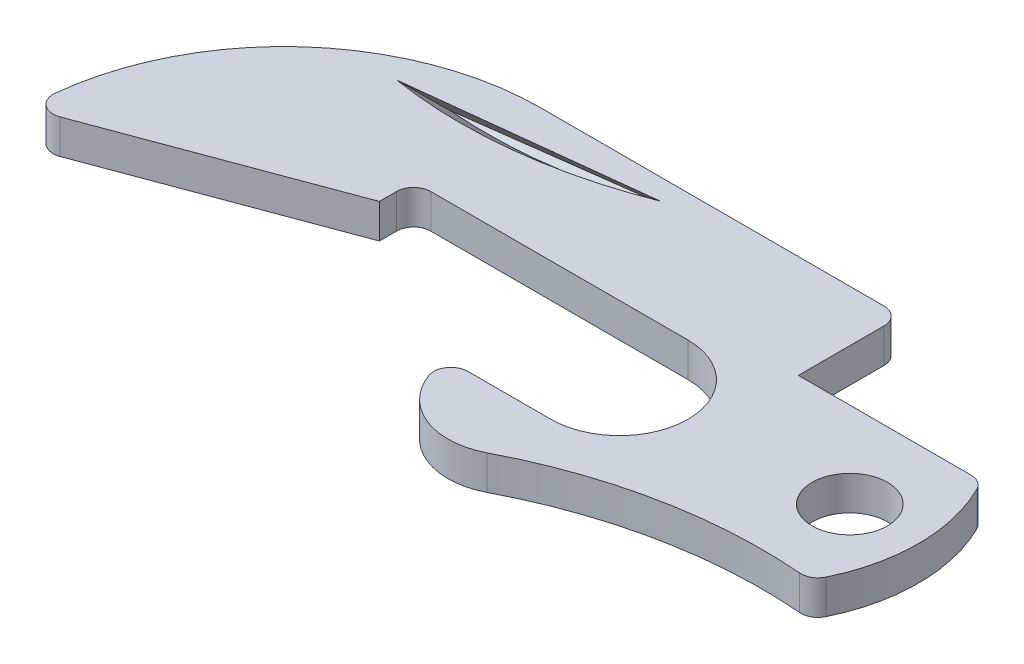
SolidWorks part; units mm, degrees
material "Stainless Steel (ferritic)"
ref_plane "Front Plane" through (0, 0, 0) normal (0, 0, 1) x (1, 0, 0)
ref_plane "Top Plane" through (0, 0, 0) normal (0, 1, 0) x (1, 0, 0)
ref_plane "Right Plane" through (0, 0, 0) normal (1, 0, 0) x (0, 0, -1)
sketch "Sketch1" plane through (0, 0, 0) normal (0, 1, 0) x (1, 0, 0)
  line L0 (0, 0) -> (-6.7693, 0)
  line L1 (-6.7693, 0) -> (-6.7693, 3.81)
  line L2 (-6.7693, 3.81) -> (-20.1043, 3.81)
  line L3 (-29.6293, -5.715) -> (-20.1043, -2.1795)
  line L4 (-20.1043, -2.1795) -> (-20.1043, -0.9095)
  line L5 (-20.1043, -0.9095) -> (-9.9443, -0.9095)
  line L6 (-9.9443, -5.9895) -> (-13.7543, -5.9895)
  line L7 (-29.6293, -5.715) -> (-29.6293, 7.3662) construction
  arc A0 (-20.1043, 3.81) -> (-29.6293, -5.715) centre (-20.1043, -5.715) ccw
  arc A1 (-9.9443, -0.9095) -> (-9.9443, -5.9895) centre (-9.9443, -3.4495) cw
  arc A4 (-10.0458, -8.2448) -> (0, -6.35) centre (-1.8666, -24.0317) cw
  arc A5 (0, -6.35) -> (0, 0) centre (-5.4993, -3.175) ccw
  arc A6 (-13.7543, -5.9895) -> (-10.0458, -8.2448) centre (-11.2143, -5.9895) ccw
  circle A7 centre (-1.6893, -3.175) radius 1.397
  point P19 (-7.4043, -3.4495)
  point P22 (0.8507, -3.175)
  dimension "D2" = 6.35
  dimension "D6" = 2.54
  dimension "D8" = 17.78
  dimension "D9" = 2.54
  dimension "D10" = 9.525
  dimension "D14" = 2.794
  dimension "D1" = 6.35
  dimension "D3" = 30.48
  dimension "D4" = 3.81
  dimension "D5" = 3.81
  dimension "D7" = 7.62
  dimension "D11" = 10.16
  dimension "D12" = 6.35
  dimension "D13" = 1.27
  dimension "D15" = 2.54
extrude "Boss-Extrude1" add sketch "Sketch1" along normal blind 1.27
fillet "Fillet1" radius 0.635 6 edges at (-6.7693, 0.635, -3.81) (-29.6293, 0.635, 5.715) (0, 0.635, 0) (0, 0.635, 6.35) (-13.7543, 0.635, 5.9895) (-20.1043, 0.635, 0.9095)
ref_plane "Plane1" through (0, 0.4547, 0.4547) normal (0, 0.7071, 0.7071) x (1, 0, 0)
sketch "Sketch3" plane through (0, 0.4547, 0.4547) normal (0, 0.7071, 0.7071) x (1, 0, 0)
  line L0 (-24.6696, 2.3535) -> (-13.2396, 3.3535)
  line L1 (-7.4043, 3.5921) -> (-20.1043, 3.5921) construction
  arc A0 (-24.6696, 2.3535) -> (-13.2396, 3.3535) centre (-21.1111, 27.503) ccw
  dimension "D2" = 25.4
  dimension "D1" = 11.43
  dimension "D3" = 5
extrude "Cut-Extrude3" cut sketch "Sketch3" against normal blind 2.286 draft 5
